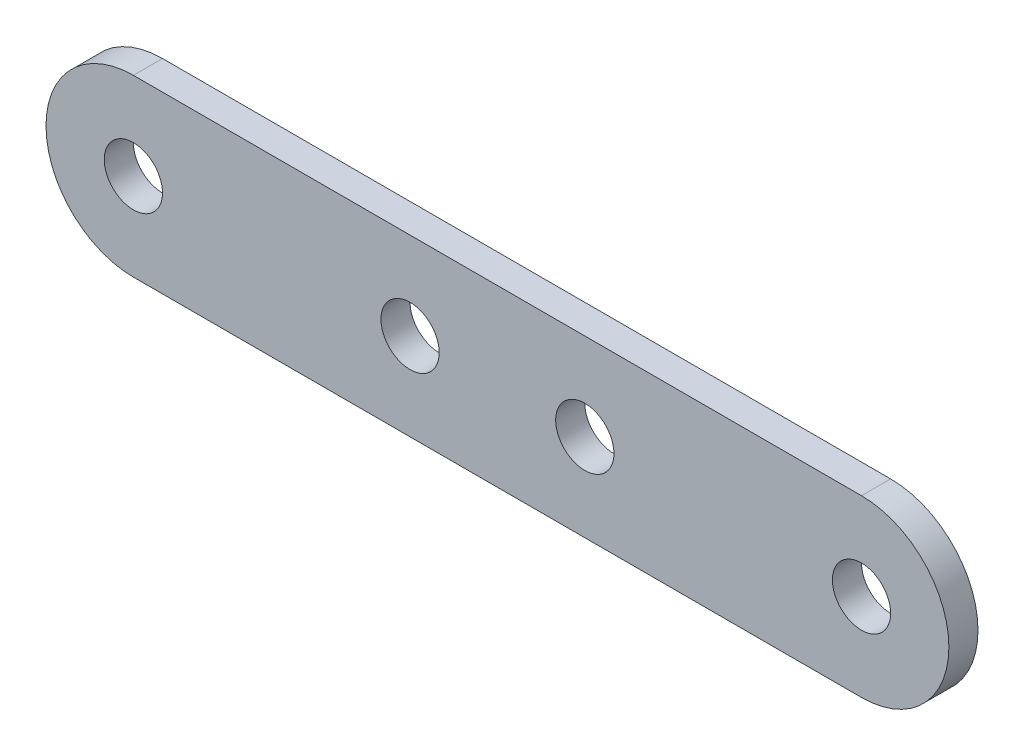
SolidWorks part; units mm, degrees
ref_plane "Plan de face" through (0, 0, 0) normal (0, 0, 1) x (1, 0, 0)
ref_plane "Plan de dessus" through (0, 0, 0) normal (0, 1, 0) x (1, 0, 0)
ref_plane "Plan de droite" through (0, 0, 0) normal (1, 0, 0) x (0, 0, -1)
sketch "Esquisse1" plane through (0, 0, 0) normal (0, 0, 1) x (1, 0, 0)
  line L1 (6, 0) -> (56, 0)
  line L2 (0, 0) -> (0, -6)
  line L3 (6, -12) -> (56, -12)
  circle A0 centre (6, -6) radius 2
  circle A1 centre (25, -6) radius 2
  circle A2 centre (37, -6) radius 2
  circle A3 centre (56, -6) radius 2
  arc A4 (6, 0) -> (6, -12) centre (6, -6) ccw
  arc A5 (56, -12) -> (56, 0) centre (56, -6) ccw
  point P1 (62, -6)
  dimension "D5" = 4
  dimension "D6" = 6
  dimension "D8" = 4
  dimension "D9" = 4
  dimension "D10" = 4
  dimension "D17" = 12
  dimension "D18" = 6
  dimension "D19" = 6
  dimension "D20" = 12
  dimension "D21" = 62
  dimension "D3" = 0
  dimension "D4" = 0
  dimension "D7" = 6
  dimension "D11" = 6
  dimension "D12" = 6
  dimension "D13" = 6
  dimension "D14" = 25
  dimension "D15" = 12
  dimension "D16" = 25
extrude "Boss.-Extru.1" add sketch "Esquisse1" against normal blind 2 contours L3 A5 L1 A4 A0 A1 A2 A3
